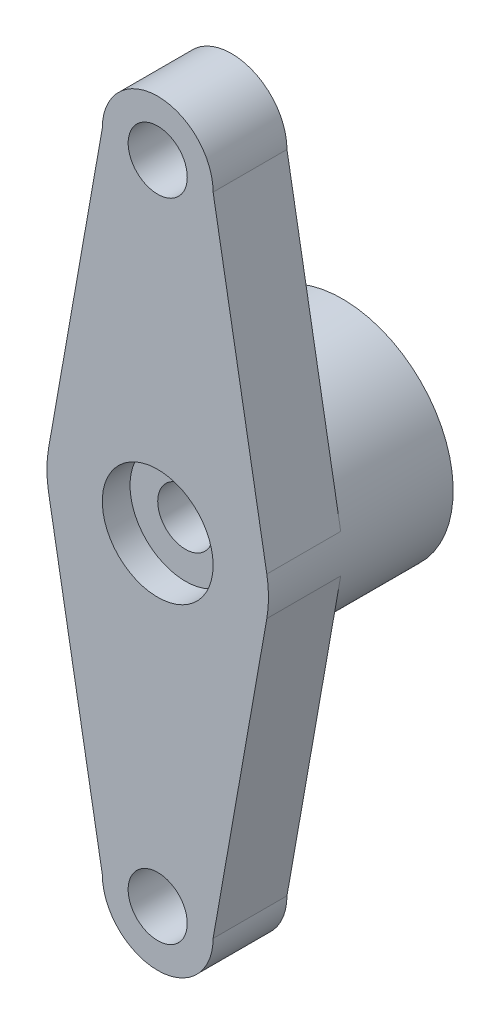
SolidWorks part; units mm, degrees
ref_plane "Front Plane" through (0, 0, 0) normal (0, 0, 1) x (1, 0, 0)
ref_plane "Top Plane" through (0, 0, 0) normal (0, 1, 0) x (1, 0, 0)
ref_plane "Right Plane" through (0, 0, 0) normal (1, 0, 0) x (0, 0, -1)
sketch "Sketch1" plane through (0, 0, 0) normal (0, 0, 1) x (1, 0, 0)
  line L0 (3, 17.5) -> (5.9084, 1.0443)
  line L1 (-3, 17.5) -> (-5.9084, 1.0443)
  line L2 (-5.9084, -1.0443) -> (-3, -17.5)
  line L3 (3, -17.5) -> (5.9084, -1.0443)
  arc A0 (5.9084, -1.0443) -> (5.9084, 1.0443) centre (0, 0) ccw
  arc A1 (3, 17.5) -> (-3, 17.5) centre (0, 17.5) ccw
  arc A2 (-3, -17.5) -> (3, -17.5) centre (0, -17.5) ccw
  arc A3 (-5.9084, 1.0443) -> (-5.9084, -1.0443) centre (0, 0) ccw
  dimension "D1" = 6
  dimension "D2" = 6
  dimension "D3" = 12
  dimension "D4" = 17.5
  dimension "D5" = 17.5
sketch "Sketch2" plane through (0, 0, 0) normal (0, 0, 1) x (1, 0, 0)
  line L0 (-2.9556, 18.0143) -> (-5.9112, 1.0286)
  line L1 (5.9112, -1.0286) -> (2.9556, -18.0143)
  line L2 (2.9556, 18.0143) -> (5.9112, 1.0286)
  line L3 (-5.9112, -1.0286) -> (-2.9556, -18.0143)
  circle A0 centre (0, 17.5) radius 3 construction
  circle A1 centre (0, 0) radius 6 construction
  circle A3 centre (0, -17.5) radius 3 construction
extrude "Boss-Extrude1" add sketch "Sketch1" against normal blind 4
sketch "Sketch4" plane through (0, 0, 0) normal (0, 0, 1) x (1, 0, 0)
  circle A0 centre (0, 17.5) radius 1.6
  circle A1 centre (0, -17.5) radius 1.6
  dimension "D1" = 3.2
  dimension "D2" = 3.2
  dimension "D3" = 17.5
  dimension "D4" = 17.5
sketch "Sketch5" plane through (0, 0, -4) normal (0, 0, -1) x (-1, 0, 0)
  circle A0 centre (0, 0) radius 6
extrude "Boss-Extrude3" add sketch "Sketch5" along normal blind 6
sketch "Sketch6" plane through (0, 0, -10) normal (0, 0, -1) x (-1, 0, 0)
  circle A0 centre (0, 0) radius 3
  dimension "D1" = 6
extrude "Cut-Extrude1" cut sketch "Sketch6" against normal blind 5
sketch "Sketch7" plane through (0, 0, -5) normal (0, 0, -1) x (-1, 0, 0)
  circle A0 centre (0, 0) radius 1.5
  dimension "D1" = 3
extrude "Cut-Extrude2" cut sketch "Sketch7" against normal through all
extrude "Cut-Extrude3" cut sketch "Sketch4" against normal through all
sketch "Sketch8" plane through (0, 0, 0) normal (0, 0, 1) x (1, 0, 0)
  circle A0 centre (0, 0) radius 3
  dimension "D1" = 6
extrude "Cut-Extrude4" cut sketch "Sketch8" against normal blind 1.5
